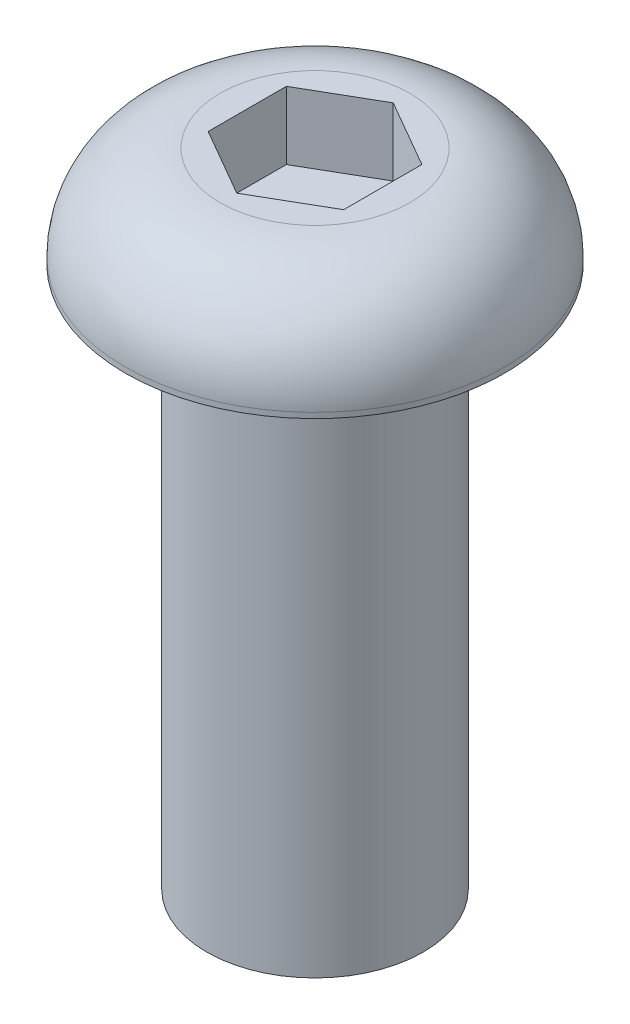
SolidWorks part; units mm, degrees
ref_plane "Plano frontal" through (0, 0, 0) normal (0, 0, 1) x (1, 0, 0)
ref_plane "Plano superior" through (0, 0, 0) normal (0, 1, 0) x (1, 0, 0)
ref_plane "Plano direito" through (0, 0, 0) normal (1, 0, 0) x (0, 0, -1)
sketch "Esboço1" plane through (0, 0, 0) normal (0, 0, 1) x (1, 0, 0)
  line L0 (0, 0) -> (8, 0)
  line L1 (8, 0) -> (8, 40)
  line L2 (8, 40) -> (14, 40)
  line L3 (14, 40) -> (14, 40.4)
  line L4 (7, 47.4) -> (0, 47.4)
  line L5 (0, 47.4) -> (0, 0) construction
  line L6 (0, 0) -> (0, 47.4)
  arc A0 (14, 40.4) -> (7, 47.4) centre (7, 40.4) ccw
  dimension "D1" = 28
  dimension "D2" = 16
  dimension "D3" = 14
  dimension "D4" = 40
  dimension "D5" = 0.4
revolve "Revolução1" add sketch "Esboço1" angle 360 about L5
sketch "Esboço2" plane through (0, 47.4, 0) normal (0, 1, 0) x (1, 0, 0)
  line L1 (0, 5.7735) -> (-5, 2.8868)
  line L2 (-5, 2.8868) -> (-5, -2.8868)
  line L3 (-5, -2.8868) -> (0, -5.7735)
  line L4 (0, -5.7735) -> (5, -2.8868)
  line L5 (5, -2.8868) -> (5, 2.8868)
  line L6 (5, 2.8868) -> (0, 5.7735)
  circle A0 centre (0, 0) radius 5 construction
  dimension "D1" = 10
extrude "Corte-extrusão1" cut sketch "Esboço2" against normal blind 5
